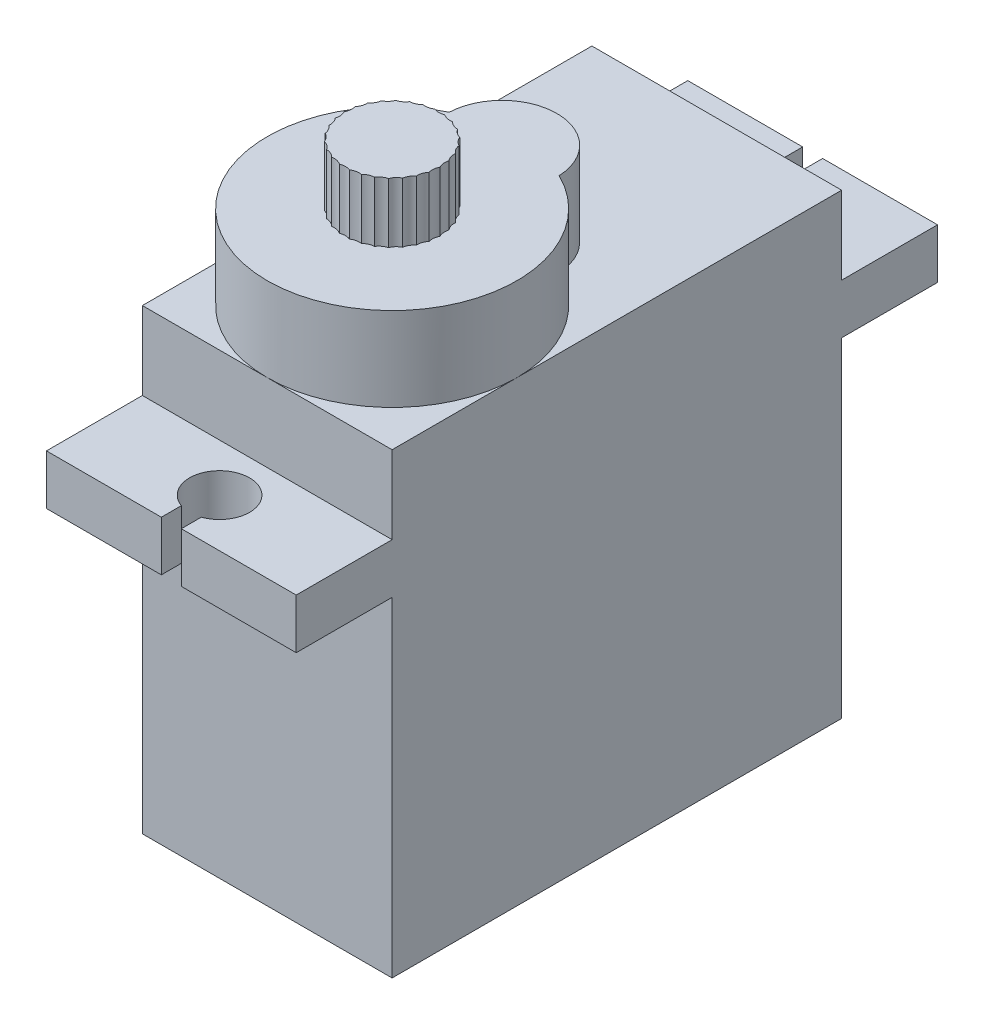
SolidWorks part; units mm, degrees
material "PBTP"
ref_plane "Front Plane" through (0, 0, 0) normal (0, 0, 1) x (1, 0, 0)
ref_plane "Top Plane" through (0, 0, 0) normal (0, 1, 0) x (1, 0, 0)
ref_plane "Right Plane" through (0, 0, 0) normal (1, 0, 0) x (0, 0, -1)
sketch "Sketch1" plane through (0, 0, 0) normal (0, 1, 0) x (1, 0, 0)
  line L0 (-6.25, -11.25) -> (6.25, 11.25) construction
  line L1 (-6.25, 11.25) -> (6.25, 11.25)
  line L2 (-6.25, 11.25) -> (-6.25, -11.25)
  line L3 (-6.25, -11.25) -> (6.25, -11.25)
  line L4 (6.25, 11.25) -> (6.25, -11.25)
  line L5 (-6.25, 11.25) -> (6.25, -11.25) construction
  point P4 (0, 0)
  dimension "D1" = 12.5
  dimension "D2" = 22.5
extrude "Boss-Extrude1" add sketch "Sketch1" along normal blind 19
sketch "Sketch2" plane through (0, 19, 0) normal (0, 1, 0) x (1, 0, 0)
  line L1 (-6.25, 16.05) -> (6.25, 16.05)
  line L2 (-6.25, 16.05) -> (-6.25, -16.05)
  line L3 (-6.25, -16.05) -> (6.25, -16.05)
  line L4 (6.25, 16.05) -> (6.25, -16.05)
  line L5 (-6.25, 11.25) -> (-6.25, -11.25) construction
  line L6 (6.25, -11.25) -> (6.25, 11.25) construction
  line L7 (6.25, 16.05) -> (-6.25, -16.05) construction
  line L8 (6.25, -16.05) -> (-6.25, 16.05) construction
  point P8 (0, 0)
  dimension "D1" = 32.1
extrude "Boss-Extrude2" add sketch "Sketch2" against normal blind 2.5
sketch "Sketch3" plane through (0, 19, 0) normal (0, 1, 0) x (1, 0, 0)
  line L4 (6.25, 11.25) -> (-6.25, 11.25)
  line L5 (6.25, -11.25) -> (6.25, 11.25)
  line L6 (-6.25, -11.25) -> (6.25, -11.25)
  line L7 (-6.25, 11.25) -> (-6.25, -11.25)
  line L8 (6.25, 11.25) -> (-6.25, 11.25)
  line L9 (6.25, -11.25) -> (6.25, 11.25)
  line L10 (-6.25, -11.25) -> (6.25, -11.25)
  line L11 (-6.25, 11.25) -> (-6.25, -11.25)
  dimension "D1" = 0
extrude "Boss-Extrude3" add sketch "Sketch3" along normal blind 3.9
sketch "Sketch4" plane through (0, 22.9, 0) normal (0, 1, 0) x (1, 0, 0)
  line L0 (-6.25, -11.25) -> (6.25, -11.25) construction
  line L1 (6.25, -11.25) -> (6.25, 11.25) construction
  line L2 (-6.25, 11.25) -> (-6.25, -11.25) construction
  line L3 (0, -5) -> (0, 0.4976) construction
  arc A0 (-2.75, 0.6125) -> (2.75, 0.6125) centre (0, -5) ccw
  arc A1 (-2.75, 0.6125) -> (2.75, 0.6125) centre (0, 0.4976) cw
  point P14 (0, 3.25)
  point P15 (0, 0)
  point P16 (0, 3.7219)
  point P17 (0, 0)
  dimension "D1" = 5.5
  dimension "D2" = 14.5
extrude "Boss-Extrude4" add sketch "Sketch4" along normal blind 4.2
sketch "Sketch5" plane through (0, 27.1, 0) normal (0, 1, 0) x (1, 0, 0)
  line L0 (-2.4, -5) -> (2.4, -5) construction
  line L1 (0, -5) -> (0, -2.6131) construction
  line L2 (0, -5) -> (-0.25, -2.6131) construction
  line L3 (0.25, -2.6131) -> (0, -5) construction
  line L4 (-0.25, -2.6131) -> (0.25, -2.6131) construction
  arc A0 (-0.25, -2.6131) -> (-0.2517, -2.6132) centre (0, -5) ccw
  arc A1 (-0.25, -2.6131) -> (0.25, -2.6131) centre (0, -2.0131) ccw
  arc A2 (0.2517, -2.6132) -> (0.7408, -2.7172) centre (0.621, -2.0783) ccw
  arc A3 (0.7425, -2.7177) -> (1.1992, -2.9211) centre (1.2149, -2.2713) ccw
  arc A4 (1.2008, -2.922) -> (1.6053, -3.2159) centre (1.7557, -2.5835) ccw
  arc A5 (1.6066, -3.217) -> (1.9411, -3.5886) centre (2.2197, -3.0013) ccw
  arc A6 (1.9422, -3.59) -> (2.1922, -4.023) centre (2.5868, -3.5065) ccw
  arc A7 (2.1929, -4.0246) -> (2.3474, -4.5002) centre (2.8408, -4.077) ccw
  arc A8 (2.3477, -4.5019) -> (2.4, -4.9991) centre (2.9706, -4.6878) ccw
  arc A9 (2.4, -5.0009) -> (2.3477, -5.4981) centre (2.9706, -5.3122) ccw
  arc A10 (2.3474, -5.4998) -> (2.1929, -5.9754) centre (2.8408, -5.923) ccw
  arc A11 (2.1922, -5.977) -> (1.9422, -6.41) centre (2.5868, -6.4935) ccw
  arc A12 (1.9411, -6.4114) -> (1.6066, -6.783) centre (2.2197, -6.9987) ccw
  arc A13 (1.6053, -6.7841) -> (1.2008, -7.078) centre (1.7557, -7.4165) ccw
  arc A14 (1.1992, -7.0789) -> (0.7425, -7.2823) centre (1.2149, -7.7287) ccw
  arc A15 (0.7408, -7.2828) -> (0.2517, -7.3868) centre (0.621, -7.9217) ccw
  arc A16 (0.25, -7.3869) -> (-0.25, -7.3869) centre (0, -7.9869) ccw
  arc A17 (-0.2517, -7.3868) -> (-0.7408, -7.2828) centre (-0.621, -7.9217) ccw
  arc A18 (-0.7425, -7.2823) -> (-1.1992, -7.0789) centre (-1.2149, -7.7287) ccw
  arc A19 (-1.2008, -7.078) -> (-1.6053, -6.7841) centre (-1.7557, -7.4165) ccw
  arc A20 (-1.6066, -6.783) -> (-1.9411, -6.4114) centre (-2.2197, -6.9987) ccw
  arc A21 (-1.9422, -6.41) -> (-2.1922, -5.977) centre (-2.5868, -6.4935) ccw
  arc A22 (-2.1929, -5.9754) -> (-2.3474, -5.4998) centre (-2.8408, -5.923) ccw
  arc A23 (-2.3477, -5.4981) -> (-2.4, -5.0009) centre (-2.9706, -5.3122) ccw
  arc A24 (-2.4, -4.9991) -> (-2.3477, -4.5019) centre (-2.9706, -4.6878) ccw
  arc A25 (-2.3474, -4.5002) -> (-2.1929, -4.0246) centre (-2.8408, -4.077) ccw
  arc A26 (-2.1922, -4.023) -> (-1.9422, -3.59) centre (-2.5868, -3.5065) ccw
  arc A27 (-1.9411, -3.5886) -> (-1.6066, -3.217) centre (-2.2197, -3.0013) ccw
  arc A28 (-1.6053, -3.2159) -> (-1.2008, -2.922) centre (-1.7557, -2.5835) ccw
  arc A29 (-1.1992, -2.9211) -> (-0.7425, -2.7177) centre (-1.2149, -2.2713) ccw
  arc A30 (-0.7408, -2.7172) -> (-0.2517, -2.6132) centre (-0.621, -2.0783) ccw
  arc A31 (-1.6053, -3.2159) -> (-1.6066, -3.217) centre (0, -5) ccw
  arc A32 (-1.9411, -3.5886) -> (-1.9422, -3.59) centre (0, -5) ccw
  arc A33 (-2.1922, -4.023) -> (-2.1929, -4.0246) centre (0, -5) ccw
  arc A34 (-2.3474, -4.5002) -> (-2.3477, -4.5019) centre (0, -5) ccw
  arc A35 (-2.4, -4.9991) -> (-2.4, -5.0009) centre (0, -5) ccw
  arc A36 (-2.1929, -5.9754) -> (-2.1922, -5.977) centre (0, -5) ccw
  arc A37 (-1.9422, -6.41) -> (-1.9411, -6.4114) centre (0, -5) ccw
  arc A38 (-1.6066, -6.783) -> (-1.6053, -6.7841) centre (0, -5) ccw
  arc A39 (-1.2008, -7.078) -> (-1.1992, -7.0789) centre (0, -5) ccw
  arc A40 (-0.7425, -7.2823) -> (-0.7408, -7.2828) centre (0, -5) ccw
  arc A41 (-2.3477, -5.4981) -> (-2.3474, -5.4998) centre (0, -5) ccw
  arc A42 (-0.2517, -7.3868) -> (-0.25, -7.3869) centre (0, -5) ccw
  arc A43 (0.25, -7.3869) -> (0.2517, -7.3868) centre (0, -5) ccw
  arc A44 (0.7408, -7.2828) -> (0.7425, -7.2823) centre (0, -5) ccw
  arc A45 (1.1992, -7.0789) -> (1.2008, -7.078) centre (0, -5) ccw
  arc A46 (1.6053, -6.7841) -> (1.6066, -6.783) centre (0, -5) ccw
  arc A47 (1.9411, -6.4114) -> (1.9422, -6.41) centre (0, -5) ccw
  arc A48 (2.1922, -5.977) -> (2.1929, -5.9754) centre (0, -5) ccw
  arc A49 (2.3474, -5.4998) -> (2.3477, -5.4981) centre (0, -5) ccw
  arc A50 (2.4, -5.0009) -> (2.4, -4.9991) centre (0, -5) ccw
  arc A51 (2.3477, -4.5019) -> (2.3474, -4.5002) centre (0, -5) ccw
  arc A52 (2.1929, -4.0246) -> (2.1922, -4.023) centre (0, -5) ccw
  arc A53 (1.9422, -3.59) -> (1.9411, -3.5886) centre (0, -5) ccw
  arc A54 (1.6066, -3.217) -> (1.6053, -3.2159) centre (0, -5) ccw
  arc A55 (1.2008, -2.922) -> (1.1992, -2.9211) centre (0, -5) ccw
  arc A56 (0.7425, -2.7177) -> (0.7408, -2.7172) centre (0, -5) ccw
  arc A57 (0.2517, -2.6132) -> (0.25, -2.6131) centre (0, -5) ccw
  arc A58 (-0.7408, -2.7172) -> (-0.7425, -2.7177) centre (0, -5) ccw
  arc A59 (-1.1992, -2.9211) -> (-1.2008, -2.922) centre (0, -5) ccw
  arc A60 (-2.75, 0.6125) -> (2.75, 0.6125) centre (0, -5) ccw construction
  point P2 (0, 0)
  point P3 (0, -2.6631)
  dimension "D1" = 4.8
  dimension "D2" = 0.5
  dimension "D4" = 0.05
  dimension "D3" = 30
extrude "Boss-Extrude5" add sketch "Sketch5" along normal blind 3
sketch "Sketch6" plane through (0, 19, 0) normal (0, 1, 0) x (1, 0, 0)
  line L0 (0, 20.8485) -> (0, -23.3524) construction
  line L1 (0.5, 16.05) -> (0.5, 15.05)
  line L2 (6.25, 16.05) -> (-6.25, 16.05) construction
  line L3 (-0.5, 16.05) -> (-0.5, 15.05)
  line L4 (0.5, 16.05) -> (-0.5, 16.05)
  line L5 (-15.9711, 0) -> (18.8487, 0) construction
  line L6 (-6.25, -16.05) -> (6.25, -16.05) construction
  line L7 (-0.5, -16.05) -> (-0.5, -15.05)
  line L8 (0.5, -16.05) -> (-0.5, -16.05)
  line L9 (0.5, -16.05) -> (0.5, -15.05)
  arc A0 (-0.5, 15.05) -> (0.5, 15.05) centre (0, 13.6358) ccw
  arc A1 (-0.5, -15.05) -> (0.5, -15.05) centre (0, -13.6358) cw
  dimension "D1" = 3
  dimension "D2" = 1
  dimension "D3" = 1
extrude "Cut-Extrude1" cut sketch "Sketch6" against normal through all
